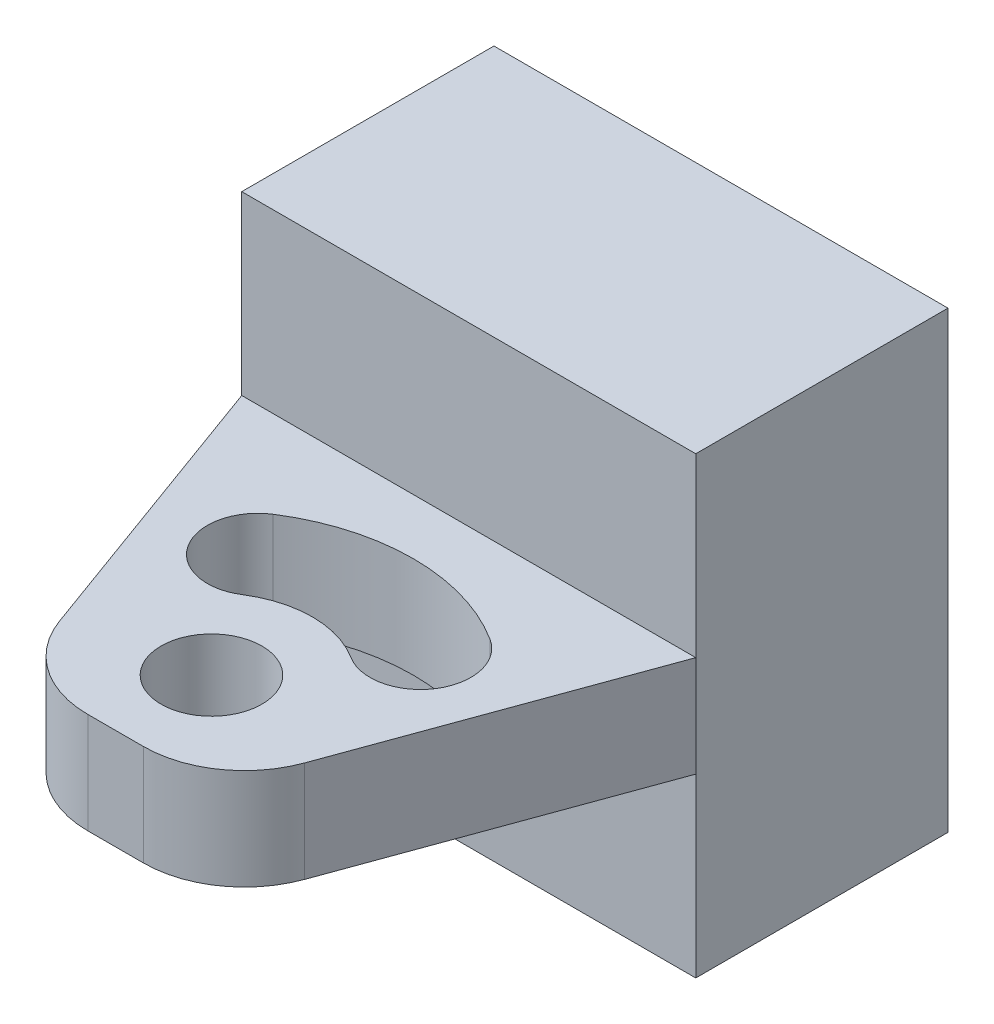
SolidWorks part; units mm, degrees
ref_plane "Front Plane" through (0, 0, 0) normal (0, 0, 1) x (1, 0, 0)
ref_plane "Top Plane" through (0, 0, 0) normal (0, 1, 0) x (1, 0, 0)
ref_plane "Right Plane" through (0, 0, 0) normal (1, 0, 0) x (0, 0, -1)
sketch "Sketch1" plane through (0, 0, 0) normal (0, 0, 1) x (1, 0, 0)
  line L1 (0, 0) -> (45, 0)
  line L2 (0, 0) -> (0, 45)
  line L3 (0, 45) -> (45, 45)
  line L4 (45, 0) -> (45, 45)
  point P5 (45, 22.5)
  dimension "D1" = 45
  dimension "D2" = 45
extrude "Boss-Extrude1" add sketch "Sketch1" along normal blind 25
sketch "Sketch3" plane through (0, 0, 25) normal (0, 0, 1) x (1, 0, 0)
  line L0 (0, 45) -> (0, 0) construction
  line L1 (0, 27.5) -> (45, 27.5)
  line L2 (0, 27.5) -> (0, 17.5)
  line L3 (0, 17.5) -> (45, 17.5)
  line L4 (45, 27.5) -> (45, 17.5)
  line L5 (45, 0) -> (45, 45) construction
  line L6 (45, 45) -> (0, 45) construction
  line L7 (0, 0) -> (45, 0) construction
  dimension "D1" = 10
  dimension "D2" = 17.5
  dimension "D3" = 17.5
extrude "Boss-Extrude2" add sketch "Sketch3" along normal blind 35
sketch "Sketch4" plane through (0, 17.5, 0) normal (0, -1, 0) x (1, 0, 0)
  line L2 (22.5, 50.5) -> (22.5, 64.7681) construction
  line L6 (0, 60) -> (0, 25) construction
  line L7 (0, 60) -> (45, 60) construction
  line L8 (14.4405, 37.8491) -> (22.5, 50.5) construction
  line L9 (22.5, 50.5) -> (30.5595, 37.8491) construction
  arc A0 (33.246, 33.6322) -> (27.873, 42.0661) centre (30.5595, 37.8491) ccw
  circle A4 centre (22.5, 50.5) radius 5
  arc A5 (17.127, 42.0661) -> (11.754, 33.6322) centre (14.4405, 37.8491) ccw
  arc A6 (17.127, 42.0661) -> (27.873, 42.0661) centre (22.5, 50.5) ccw
  arc A7 (11.754, 33.6322) -> (33.246, 33.6322) centre (22.5, 50.5) ccw
  dimension "D5" = 22.5
  dimension "D2" = 10
  dimension "D3" = 10
  dimension "D4" = 10
  dimension "D10" = 10
  dimension "D11" = 20
  dimension "D6" = 9.5
  dimension "D7" = 15
  dimension "D8" = 15
  dimension "D9" = 65
  dimension "D12" = 32.5
extrude "Cut-Extrude4" cut sketch "Sketch4" against normal through all
sketch "Sketch5" plane through (0, 0, 0) normal (0, 1, 0) x (1, 0, 0)
  line L0 (45, -25) -> (32.261, -60)
  line L1 (45, -60) -> (0, -60) construction
  line L2 (0, -25) -> (12.739, -60)
  line L3 (0, -60) -> (0, -25) construction
  line L4 (45, -60) -> (45, -25) construction
  line L5 (12.739, -60) -> (0, -60)
  line L6 (0, -60) -> (0, -25)
  line L7 (32.261, -60) -> (45, -60)
  line L8 (45, -60) -> (45, -25)
  dimension "D1" = 20
  dimension "D2" = 20
extrude "Cut-Extrude5" cut sketch "Sketch5" along normal through all
fillet "Fillet1" radius 10 2 edges at (12.739, 22.5, 60) (32.261, 22.5, 60)
